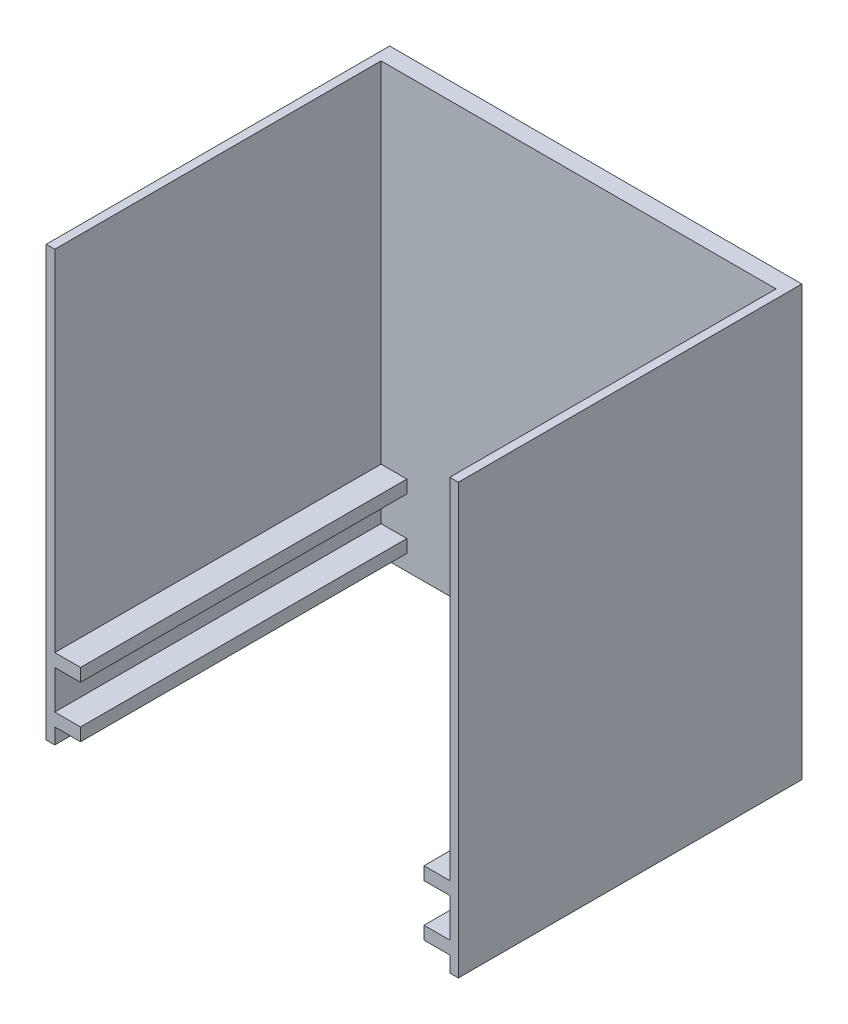
SolidWorks part; units mm, degrees
ref_plane "Front Plane" through (0, 0, 0) normal (0, 0, 1) x (1, 0, 0)
ref_plane "Top Plane" through (0, 0, 0) normal (0, 1, 0) x (1, 0, 0)
ref_plane "Right Plane" through (0, 0, 0) normal (1, 0, 0) x (0, 0, -1)
sketch "Sketch1" plane through (0, 0, 0) normal (0, 0, 1) x (1, 0, 0)
  line L1 (-24, -22.3221) -> (24, -22.3221)
  line L2 (-24, -22.3221) -> (-24, 27.6779)
  line L3 (-24, 27.6779) -> (24, 27.6779)
  line L4 (24, -22.3221) -> (24, 27.6779)
  point P1 (0, 0)
  dimension "D1" = 48
extrude "Boss-Extrude1" add sketch "Sketch1" along normal blind 40
sketch "Sketch4" plane through (0, 0, 0) normal (0, 0, 1) x (1, 0, 0)
  line L0 (-23, -19) -> (-23, -14.5)
  line L1 (23, -14.5) -> (23, -19)
  line L2 (24, 27.6779) -> (-24, 27.6779) construction
  line L3 (23, -19) -> (20, -19)
  line L4 (-23, -14.5) -> (-20, -14.5)
  line L9 (20, -19) -> (20, -20.5)
  line L10 (20, -20.5) -> (23, -20.5)
  line L11 (23, -14.5) -> (20, -14.5)
  line L12 (-20, -14.5) -> (-20, -13)
  line L13 (-20, -13) -> (-23, -13)
  line L14 (20, -14.5) -> (20, -13)
  line L15 (20, -13) -> (23, -13)
  line L16 (23, -13) -> (23, 27.6779)
  line L17 (23, 27.6779) -> (-23, 27.6779)
  line L18 (-23, 27.6779) -> (-23, -13)
  line L19 (23, -20.5) -> (23, -22.3221)
  line L20 (-24, -22.3221) -> (24, -22.3221) construction
  line L21 (23, -22.3221) -> (-23, -22.3221)
  line L22 (-23, -22.3221) -> (-23, -20.5)
  line L23 (-23, -20.5) -> (-20, -20.5)
  line L24 (-20, -20.5) -> (-20, -19)
  line L25 (-20, -19) -> (-23, -19)
  dimension "D1" = 1.5
  dimension "D2" = 4.5
  dimension "D3" = 1.5
  dimension "D4" = 4.5
  dimension "D5" = 1.5
  dimension "D6" = 1.5
extrude "Cut-Extrude5" cut sketch "Sketch4" against normal blind 38 from surface at 40 starting at face at (0, 2.6779, 40)
